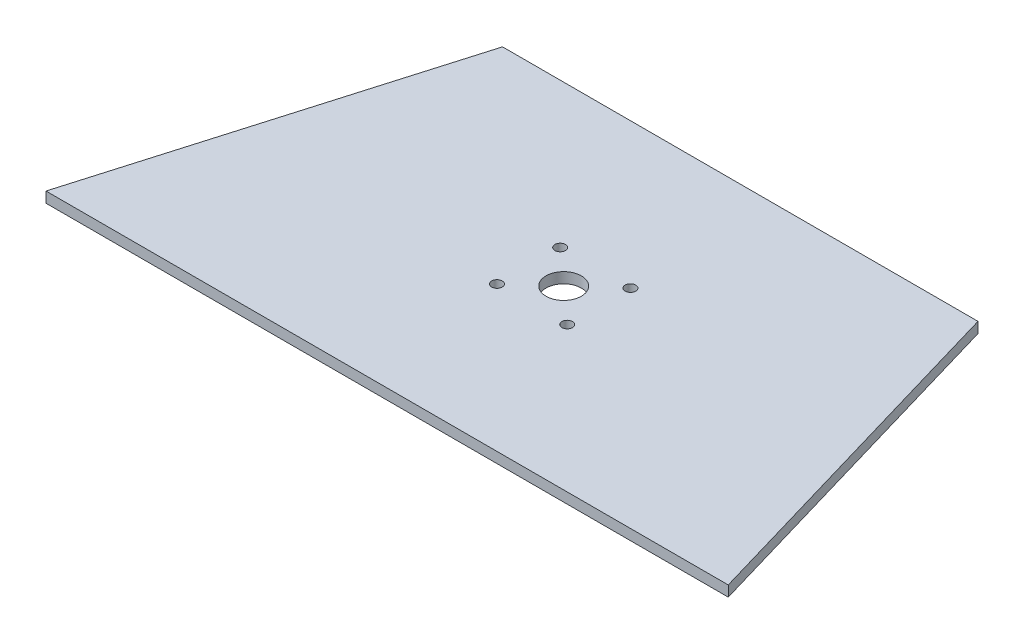
SolidWorks part; units mm, degrees
ref_plane "Front Plane" through (0, 0, 0) normal (0, 0, 1) x (1, 0, 0)
ref_plane "Top Plane" through (0, 0, 0) normal (0, 1, 0) x (1, 0, 0)
ref_plane "Right Plane" through (0, 0, 0) normal (1, 0, 0) x (0, 0, -1)
sketch "Sketch1" plane through (0, 0, 0) normal (0, 1, 0) x (1, 0, 0)
  line L0 (-13.2, 0) -> (180, 0)
  line L3 (90, 0) -> (90, 100) construction
  line L5 (-13.2, 0) -> (16.0799, 100)
  line L6 (180, 0) -> (150.7201, 100)
  line L7 (16.0799, 100) -> (150.7201, 100)
extrude "Boss-Extrude1" add sketch "Sketch1" along normal blind 3
hole_wizard "Ø10.0mm Dowel Hole1" positions "Sketch2" profile "Sketch3" hole size "Ø10.0" standard "ANSI Metric" end condition up to next
sketch "Sketch2" plane through (0, 3, 0) normal (0, 1, 0) x (1, 0, 0)
  point P0 (83.4, 50)
sketch "Sketch3" plane through (83.4, 3, -50) normal (1, 0, 0) x (0, 0, 1)
  line L0 (0, 0) -> (0, 3)
  line L1 (0, 3) -> (5, 3)
  line L2 (5, 3) -> (5, 0)
  line L5 (5, 0) -> (0, 0)
  line L11 (0, -6.35) -> (0, 107.95) construction
  dimension "Thru Hole Dia." = 10
  dimension "Thru Hole Depth" = 3
hole_wizard "Ø3.0mm Dowel Hole1" positions "Sketch4" profile "Sketch5" hole size "Ø3.0" standard "ANSI Metric" end condition up to next
sketch "Sketch4" plane through (0, 3, 0) normal (0, 1, 0) x (1, 0, 0)
  point P0 (73.45, 58.95)
  point P3 (73.45, 41.05)
  point P6 (93.35, 41.05)
  point P9 (93.35, 58.95)
sketch "Sketch5" plane through (73.45, 3, -58.95) normal (1, 0, 0) x (0, 0, 1)
  line L0 (0, 0) -> (0, 3)
  line L1 (0, 3) -> (1.5, 3)
  line L2 (1.5, 3) -> (1.5, 0)
  line L5 (1.5, 0) -> (0, 0)
  line L11 (0, -6.35) -> (0, 107.95) construction
  dimension "Thru Hole Dia." = 3
  dimension "Thru Hole Depth" = 3
